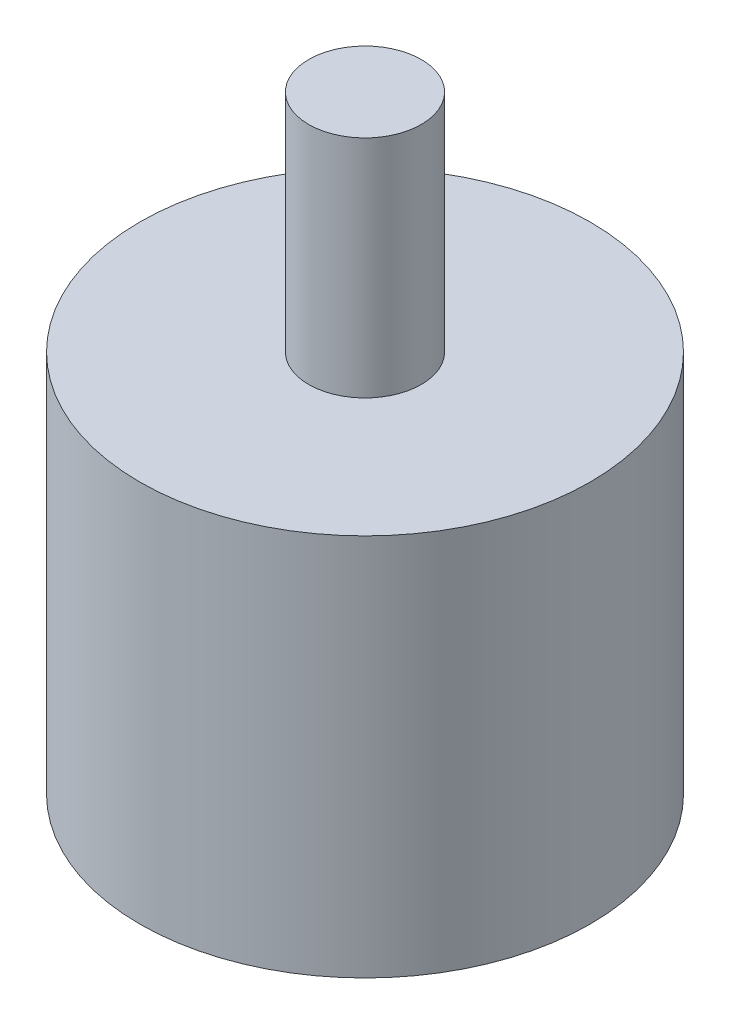
SolidWorks part; units mm, degrees
ref_plane "Ebene vorne" through (0, 0, 0) normal (0, 0, 1) x (1, 0, 0)
ref_plane "Ebene oben" through (0, 0, 0) normal (0, 1, 0) x (1, 0, 0)
ref_plane "Ebene rechts" through (0, 0, 0) normal (1, 0, 0) x (0, 0, -1)
sketch "Skizze1" plane through (0, 0, 0) normal (1, 0, 0) x (0, 0, -1)
  line L0 (-190, 208.5) -> (-190, 240.7464) construction
  line L1 (-190, 208.5) -> (-187, 208.5)
  line L2 (-187, 208.5) -> (-187, 200.5)
  line L3 (-187, 200.5) -> (-180, 200.5)
  line L4 (-180, 200.5) -> (-180, 217.5)
  line L5 (-180, 217.5) -> (-187.5, 217.5)
  line L6 (-187.5, 217.5) -> (-187.5, 227.5)
  line L7 (-187.5, 227.5) -> (-190, 227.5)
  line L9 (-190, 227.5) -> (-190, 208.5)
  line L10 (-187.5, 217.5) -> (28.841, 217.5) construction
  point P12 (0, 0)
  point P17 (-190, 227.5)
sketch "Skizze2" plane through (0, 0, 0) normal (1, 0, 0) x (0, 0, -1)
  line L0 (-190, 227.5) -> (-190, 208.5)
  line L1 (-190, 208.5) -> (-187, 208.5)
  line L2 (-187, 208.5) -> (-187, 200.5)
  line L3 (-187, 200.5) -> (-180, 200.5)
  line L4 (-180, 200.5) -> (-180, 217.5)
  line L5 (-180, 217.5) -> (-187.5, 217.5)
  line L6 (-187.5, 217.5) -> (-187.5, 227.5)
  line L7 (-187.5, 227.5) -> (-190, 227.5)
revolve "Rotation1" add sketch "Skizze2" angle 360 about L9
